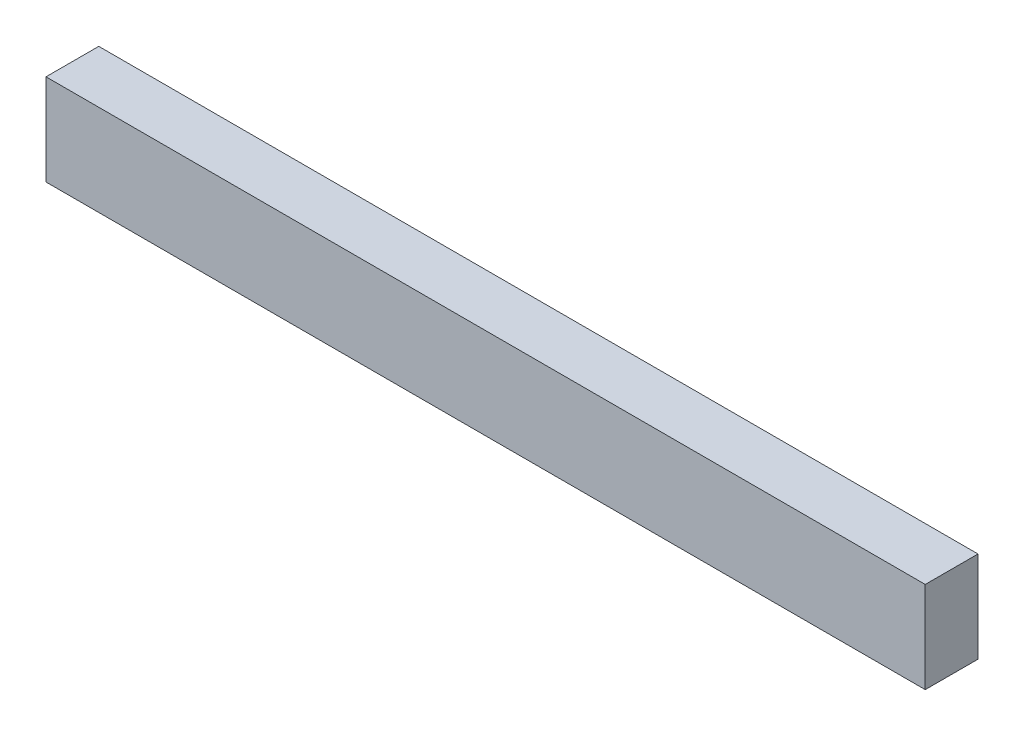
SolidWorks part; units mm, degrees
ref_plane "Front Plane" through (0, 0, 0) normal (0, 0, 1) x (1, 0, 0)
ref_plane "Top Plane" through (0, 0, 0) normal (0, 1, 0) x (1, 0, 0)
ref_plane "Right Plane" through (0, 0, 0) normal (1, 0, 0) x (0, 0, -1)
sketch "Sketch1" plane through (0, 0, 0) normal (0, 0, 1) x (1, 0, 0)
  line L1 (-63.4945, -6.5811) -> (63.4945, -6.5811)
  line L2 (-63.4945, -6.5811) -> (-63.4945, 6.5811)
  line L3 (-63.4945, 6.5811) -> (63.4945, 6.5811)
  line L4 (63.4945, -6.5811) -> (63.4945, 6.5811)
  line L5 (-63.4945, -6.5811) -> (63.4945, 6.5811) construction
  line L6 (-63.4945, 6.5811) -> (63.4945, -6.5811) construction
  point P1 (0, 0)
extrude "Boss-Extrude1" add sketch "Sketch1" along normal blind 7.62
sketch "Sketch2" plane through (0, 0, 0) normal (0, 0, -1) x (-1, 0, 0)
  circle A0 centre (52.0249, 0) radius 4.3688
extrude "Cut-Extrude1" cut sketch "Sketch2" against normal blind 4.318
